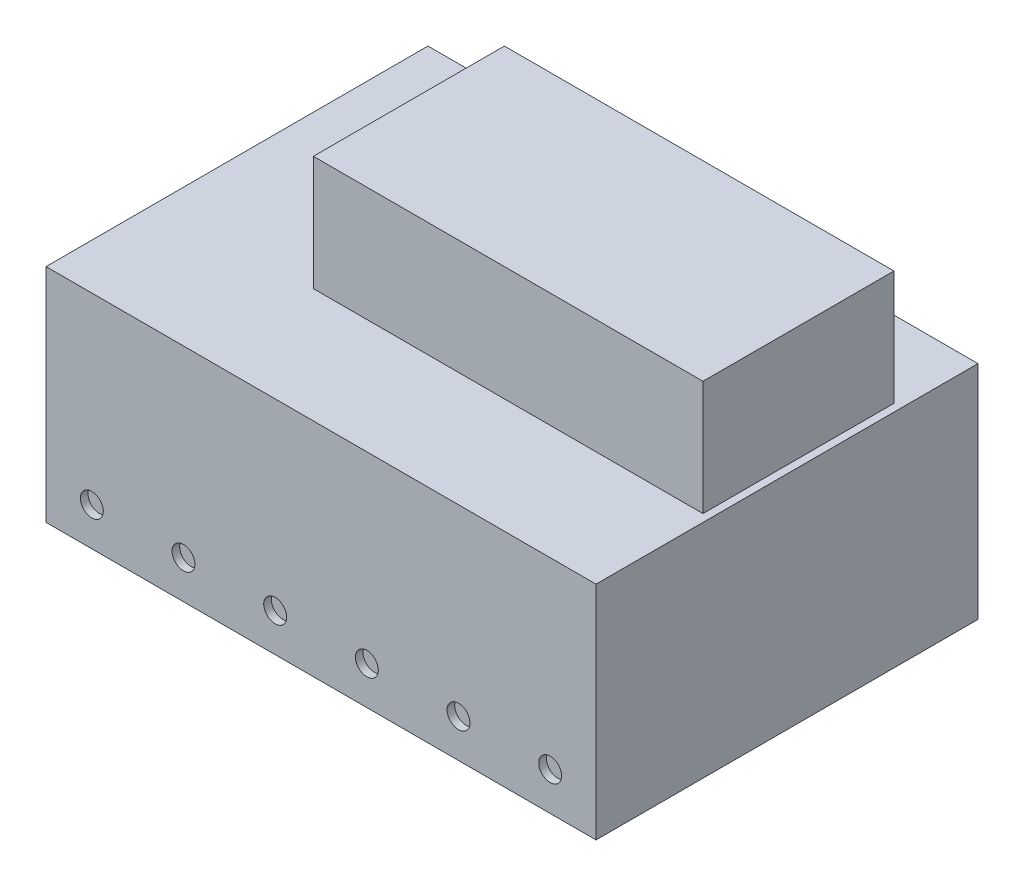
SolidWorks part; units mm, degrees
ref_plane "Front Plane" through (0, 0, 0) normal (0, 0, 1) x (1, 0, 0)
ref_plane "Top Plane" through (0, 0, 0) normal (0, 1, 0) x (1, 0, 0)
ref_plane "Right Plane" through (0, 0, 0) normal (1, 0, 0) x (0, 0, -1)
sketch "Sketch1" plane through (0, 0, 0) normal (0, 0, 1) x (1, 0, 0)
  line L1 (-36, -14.5) -> (36, -14.5)
  line L2 (-36, -14.5) -> (-36, 14.5)
  line L3 (-36, 14.5) -> (36, 14.5)
  line L4 (36, -14.5) -> (36, 14.5)
  line L5 (-36, -14.5) -> (36, 14.5) construction
  line L6 (-36, 14.5) -> (36, -14.5) construction
  point P0 (0, 0)
  dimension "D1" = 72
  dimension "D2" = 29
extrude "Boss-Extrude1" add sketch "Sketch1" along normal blind 50
sketch "Sketch2" plane through (0, 0, 50) normal (0, 0, 1) x (1, 0, 0)
  line L0 (-36, -9.5) -> (36, -9.5) construction
  line L1 (-36, 14.5) -> (-36, -14.5) construction
  line L2 (36, -14.5) -> (36, 14.5) construction
  line L3 (-36, -14.5) -> (36, -14.5) construction
  line L4 (6, -9.5) -> (-6, -9.5) construction
  line L5 (0, 0) -> (0, -14.5) construction
  circle A0 centre (-30, -9.5) radius 1.5
  circle A1 centre (-18, -9.5) radius 1.5
  circle A2 centre (-6, -9.5) radius 1.5
  circle A3 centre (6, -9.5) radius 1.5
  circle A4 centre (18, -9.5) radius 1.5
  circle A5 centre (30, -9.5) radius 1.5
  point P23 (0, -9.5)
  dimension "D2" = 6
  dimension "D4" = 3
  dimension "D1" = 5
  dimension "D3" = 12
sketch "Sketch3" plane through (0, 14.5, 0) normal (0, 1, 0) x (1, 0, 0)
  line L0 (36, 0) -> (-36, 0) construction
  line L1 (-16, -10) -> (35, -10)
  line L2 (-16, -10) -> (-16, -35)
  line L3 (-16, -35) -> (35, -35)
  line L4 (35, -10) -> (35, -35)
  line L5 (-36, -50) -> (-36, 0) construction
  line L7 (36, -50) -> (36, 0) construction
  line L8 (-36, -5) -> (36, -5) construction
  circle A0 centre (-26, -5) radius 2.5
  circle A1 centre (26, -5) radius 2.5
  dimension "D6" = 5
  dimension "D7" = 10
  dimension "D8" = 5
  dimension "D9" = 10
  dimension "D1" = 25
  dimension "D2" = 20
  dimension "D3" = 1
  dimension "D4" = 10
  dimension "D5" = 5
extrude "Boss-Extrude3" add sketch "Sketch3" along normal blind 15
extrude "Cut-Extrude1" cut sketch "Sketch2" against normal blind 1
sketch "Sketch4" plane through (0, 14.5, 0) normal (0, 1, 0) x (1, 0, 0)
  circle A0 centre (26, -5) radius 2.5 construction
  circle A1 centre (-26, -5) radius 2.5 construction
  circle A2 centre (26, -5) radius 2.5
  circle A3 centre (-26, -5) radius 2.5
extrude "Cut-Extrude2" cut sketch "Sketch4" against normal blind 40 and the other way blind 40
